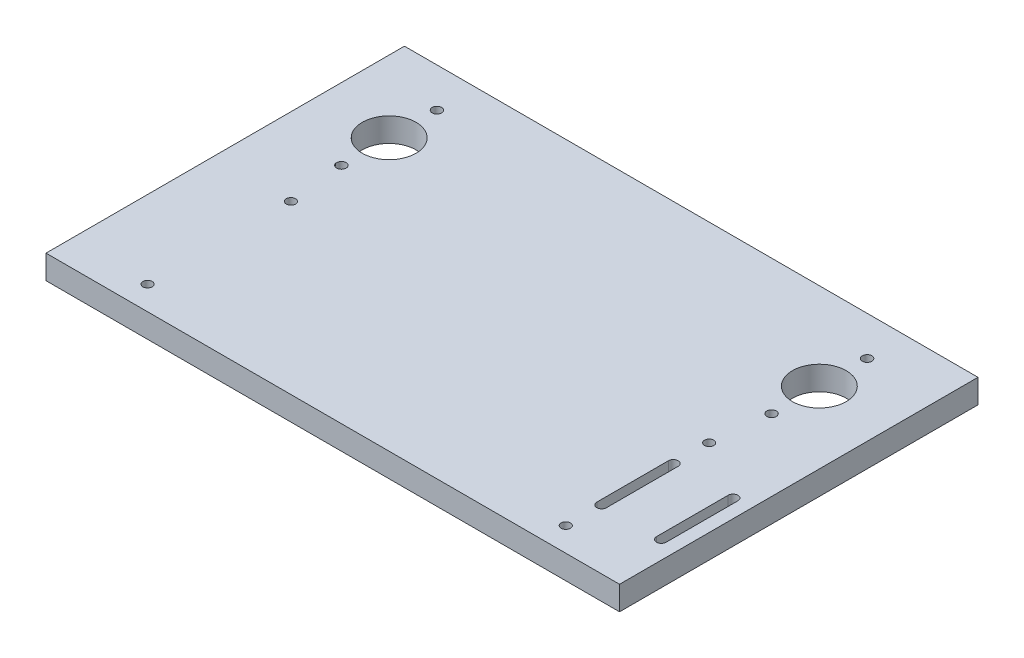
SolidWorks part; units mm, degrees
material "Pine"
ref_plane "Front Plane" through (0, 0, 0) normal (0, 0, 1) x (1, 0, 0)
ref_plane "Top Plane" through (0, 0, 0) normal (0, 1, 0) x (1, 0, 0)
ref_plane "Right Plane" through (0, 0, 0) normal (1, 0, 0) x (0, 0, -1)
sketch "Sketch1" plane through (0, 0, 0) normal (0, 1, 0) x (1, 0, 0)
  line L0 (-152.4, 87.122) -> (-114.3, 87.122) construction
  line L1 (-152.4, 133.35) -> (152.4, 133.35)
  line L2 (-152.4, 133.35) -> (-152.4, -133.35)
  line L3 (-152.4, -133.35) -> (-88.9, -133.35)
  line L4 (152.4, 133.35) -> (152.4, -133.35)
  line L5 (-152.4, 133.35) -> (152.4, -133.35) construction
  line L6 (-152.4, -133.35) -> (152.4, 133.35) construction
  line L7 (114.3, 87.122) -> (152.4, 87.122) construction
  line L8 (-88.9, -133.35) -> (-88.9, -57.15)
  line L9 (-88.9, -57.15) -> (88.9, -57.15)
  line L10 (88.9, -57.15) -> (88.9, -133.35)
  line L11 (88.9, -133.35) -> (152.4, -133.35)
  line L12 (-114.3, 112.522) -> (-114.3, 87.122) construction
  line L13 (-114.3, 87.122) -> (-114.3, 61.722) construction
  line L14 (0, 133.35) -> (0, -57.15) construction
  line L15 (114.3, 112.522) -> (114.3, 87.122) construction
  line L16 (114.3, 87.122) -> (114.3, 61.722) construction
  line L17 (-152.4, -57.15) -> (152.4, -57.15)
  circle A0 centre (-114.3, 87.122) radius 14.2748
  circle A1 centre (114.3, 87.122) radius 14.2748
  circle A2 centre (-114.3, 112.522) radius 2.54
  circle A3 centre (-114.3, 61.722) radius 2.54
  circle A4 centre (114.3, 112.522) radius 2.54
  circle A5 centre (114.3, 61.722) radius 2.54
  point P0 (0, 0)
  dimension "D3" = 28.5496
  dimension "D4" = 46.228
  dimension "D9" = 5.08
  dimension "D1" = 266.7
  dimension "D2" = 304.8
  dimension "D5" = 228.6
  dimension "D6" = 190.5
  dimension "D7" = 63.5
  dimension "D8" = 63.5
  dimension "D10" = 25.4
extrude "Boss-Extrude1" add sketch "Sketch1" along normal blind 12.7 contours L2 L17 L9 L4 L1 A4 A3 A2 A1 A0 A5
sketch "Sketch2" plane through (0, 12.7, 0) normal (0, 1, 0) x (1, 0, 0)
  line L0 (111.125, -25.4) -> (111.125, 12.7) construction
  line L1 (108.5453, -25.4) -> (108.5453, 12.7)
  line L2 (113.7047, -25.4) -> (113.7047, 12.7)
  line L3 (142.875, -25.4) -> (142.875, 12.7) construction
  line L4 (140.2953, -25.4) -> (140.2953, 12.7)
  line L5 (145.4547, -25.4) -> (145.4547, 12.7)
  line L6 (-152.4, -57.15) -> (152.4, -57.15) construction
  line L7 (152.4, 133.35) -> (152.4, -57.15) construction
  arc A4 (108.5453, -25.4) -> (113.7047, -25.4) centre (111.125, -25.4) ccw
  arc A5 (113.7047, 12.7) -> (108.5453, 12.7) centre (111.125, 12.7) ccw
  arc A6 (140.2953, -25.4) -> (145.4547, -25.4) centre (142.875, -25.4) ccw
  arc A7 (145.4547, 12.7) -> (140.2953, 12.7) centre (142.875, 12.7) ccw
  point P2 (111.125, -6.35)
  point P9 (142.875, -6.35)
  dimension "D1" = 2.5797
  dimension "D3" = 2.5797
  dimension "D2" = 38.1
  dimension "D4" = 38.1
  dimension "D5" = 31.75
  dimension "D6" = 50.8
  dimension "D7" = 9.525
extrude "Cut-Extrude2" cut sketch "Sketch2" against normal through all
sketch "Sketch3" plane through (0, 0, 0) normal (0, -1, 0) x (-1, 0, 0)
  circle A0 centre (-111.125, -44.45) radius 2.4765
  circle A1 centre (-111.125, 31.75) radius 2.4765
  circle A2 centre (111.125, 31.75) radius 2.4765
  circle A3 centre (111.125, -44.45) radius 2.4765
extrude "Cut-Extrude3" cut sketch "Sketch3" against normal through all
equation "\"D3@Sketch2\"=\"D1@Sketch2\""
equation "\"D4@Sketch2\"=\"D2@Sketch2\""
